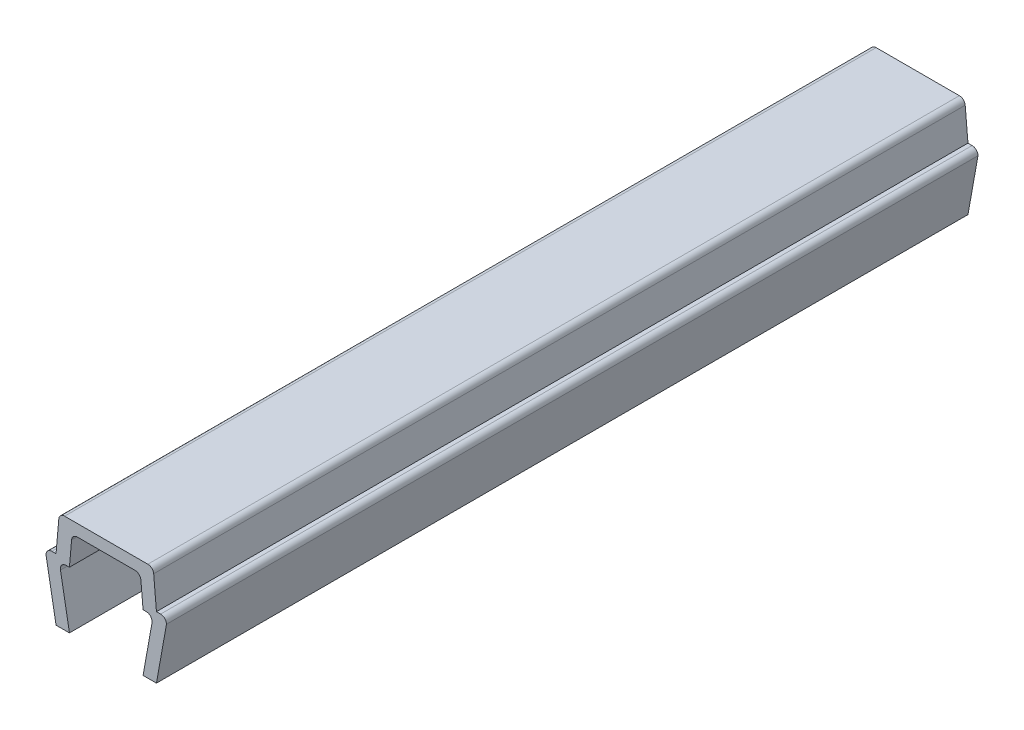
SolidWorks part; units mm, degrees
ref_plane "Front Plane" through (0, 0, 0) normal (0, 0, 1) x (1, 0, 0)
ref_plane "Top Plane" through (0, 0, 0) normal (0, 1, 0) x (1, 0, 0)
ref_plane "Right Plane" through (0, 0, 0) normal (1, 0, 0) x (0, 0, -1)
ref_plane "Plane1" through (0, 0, 0) normal (0, 0, 1) x (1, 0, 0)
sketch "Sketch1" plane through (0, 0, 0) normal (0, 0, 1) x (1, 0, 0)
  line L0 (-3.6, 3.35) -> (-3, 0)
  line L1 (-3, 0) -> (-2.2, 0)
  line L2 (-2.2, 0) -> (-2.7352, 2.9883)
  line L3 (-2.3907, 3.4) -> (-2.2, 3.4)
  line L4 (-2.2, 3.4) -> (-2.0705, 4.8805)
  line L5 (-1.7218, 5.2) -> (1.7218, 5.2)
  line L6 (2.0705, 4.8805) -> (2.2, 3.4)
  line L7 (2.2, 3.4) -> (2.3907, 3.4)
  line L8 (2.7352, 2.9883) -> (2.2, 0)
  line L9 (2.2, 0) -> (3, 0)
  line L10 (3, 0) -> (3.6, 3.35)
  line L11 (3.25, 3.7) -> (3, 3.7)
  line L12 (3, 3.7) -> (2.8355, 5.5805)
  line L13 (2.4868, 5.9) -> (-2.4868, 5.9)
  line L14 (-2.8355, 5.5805) -> (-3, 3.7)
  line L15 (-3, 3.7) -> (-3.25, 3.7)
  arc A0 (-2.7352, 2.9883) -> (-2.3907, 3.4) centre (-2.3907, 3.05) cw
  arc A1 (-2.0705, 4.8805) -> (-1.7218, 5.2) centre (-1.7218, 4.85) cw
  arc A2 (1.7218, 5.2) -> (2.0705, 4.8805) centre (1.7218, 4.85) cw
  arc A3 (2.3907, 3.4) -> (2.7352, 2.9883) centre (2.3907, 3.05) cw
  arc A4 (3.6, 3.35) -> (3.25, 3.7) centre (3.25, 3.35) ccw
  arc A5 (2.8355, 5.5805) -> (2.4868, 5.9) centre (2.4868, 5.55) ccw
  arc A6 (-2.4868, 5.9) -> (-2.8355, 5.5805) centre (-2.4868, 5.55) ccw
  arc A7 (-3.25, 3.7) -> (-3.6, 3.35) centre (-3.25, 3.35) ccw
extrude "Boss-Extrude1" add sketch "Sketch1" against normal mid plane 48.5
